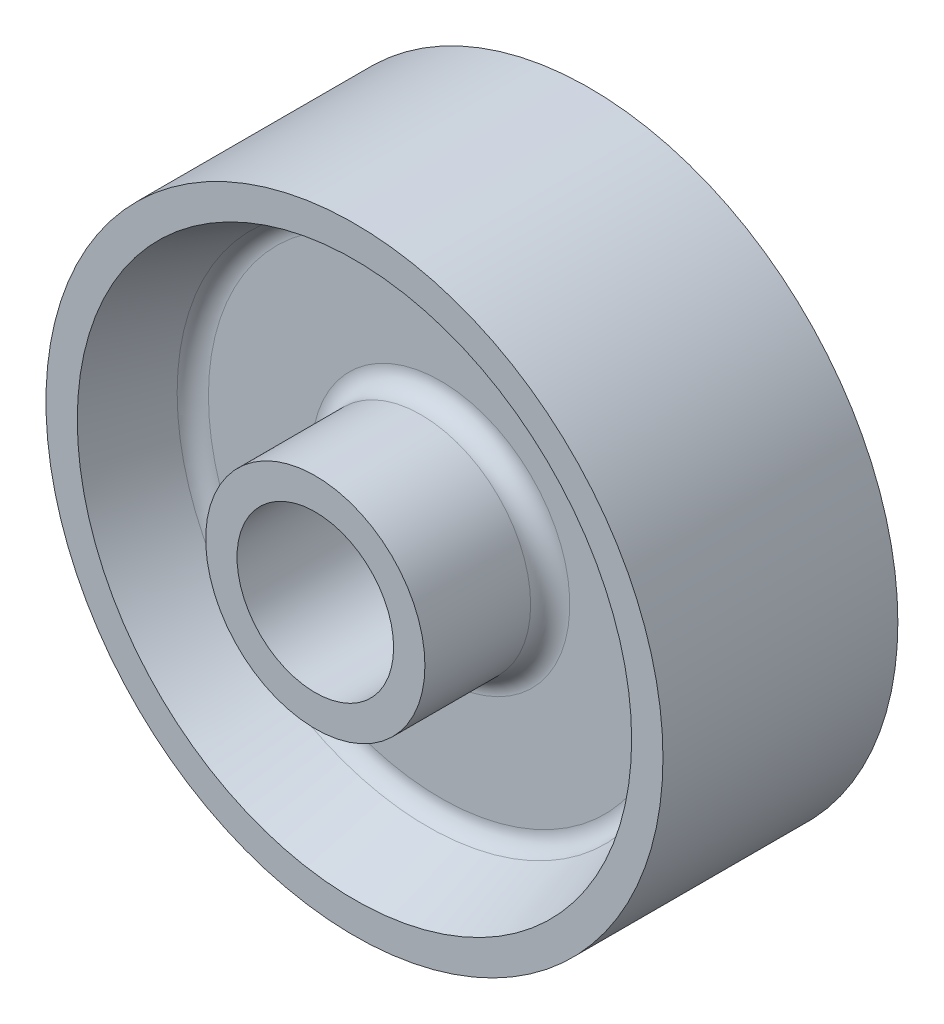
SolidWorks part; units mm, degrees
material "Gray Cast Iron"
ref_plane "Front Plane" through (0, 0, 0) normal (0, 0, 1) x (1, 0, 0)
ref_plane "Top Plane" through (0, 0, 0) normal (0, 1, 0) x (1, 0, 0)
ref_plane "Right Plane" through (0, 0, 0) normal (1, 0, 0) x (0, 0, -1)
sketch "Sketch1" plane through (0, 0, 0) normal (1, 0, 0) x (0, 0, -1)
  line L0 (-25.4, 12.7) -> (25.4, 12.7)
  line L1 (25.4, 12.7) -> (25.4, 17.78)
  line L2 (25.4, 17.78) -> (5.08, 17.78)
  line L3 (5.08, 17.78) -> (5.08, 39.878)
  line L4 (5.08, 39.878) -> (19.05, 44.958)
  line L5 (19.05, 44.958) -> (19.05, 50.038)
  line L6 (19.05, 50.038) -> (-19.05, 50.038)
  line L7 (-19.05, 50.038) -> (-19.05, 44.958)
  line L8 (-19.05, 44.958) -> (-5.08, 39.878)
  line L9 (-5.08, 39.878) -> (-5.08, 17.78)
  line L10 (-5.08, 17.78) -> (-25.4, 17.78)
  line L11 (-25.4, 17.78) -> (-25.4, 12.7)
  line L12 (-55.6731, 0) -> (70.9858, 0) construction
  dimension "D1" = 50.8
  dimension "D2" = 5.08
  dimension "D3" = 5.08
  dimension "D4" = 10.16
  dimension "D5" = 20.32
  dimension "D6" = 38.1
  dimension "D7" = 25.4
  dimension "D8" = 5.08
  dimension "D9" = 5.08
  dimension "D10" = 100.076
  dimension "D11" = 10.16
  dimension "D12" = 6.35
  dimension "D13" = 10.16
  dimension "D14" = 25.4
revolve "Revolve1" add sketch "Sketch1" angle 360 about L12
fillet "Fillet1" radius 3.175 1 edges at (17.78, 0, 5.08)
fillet "Fillet2" radius 3.175 1 edges at (39.878, 0, 5.08)
fillet "Fillet3" radius 3.175 1 edges at (17.78, 0, -5.08)
fillet "Fillet4" radius 3.175 1 edges at (39.878, 0, -5.08)
